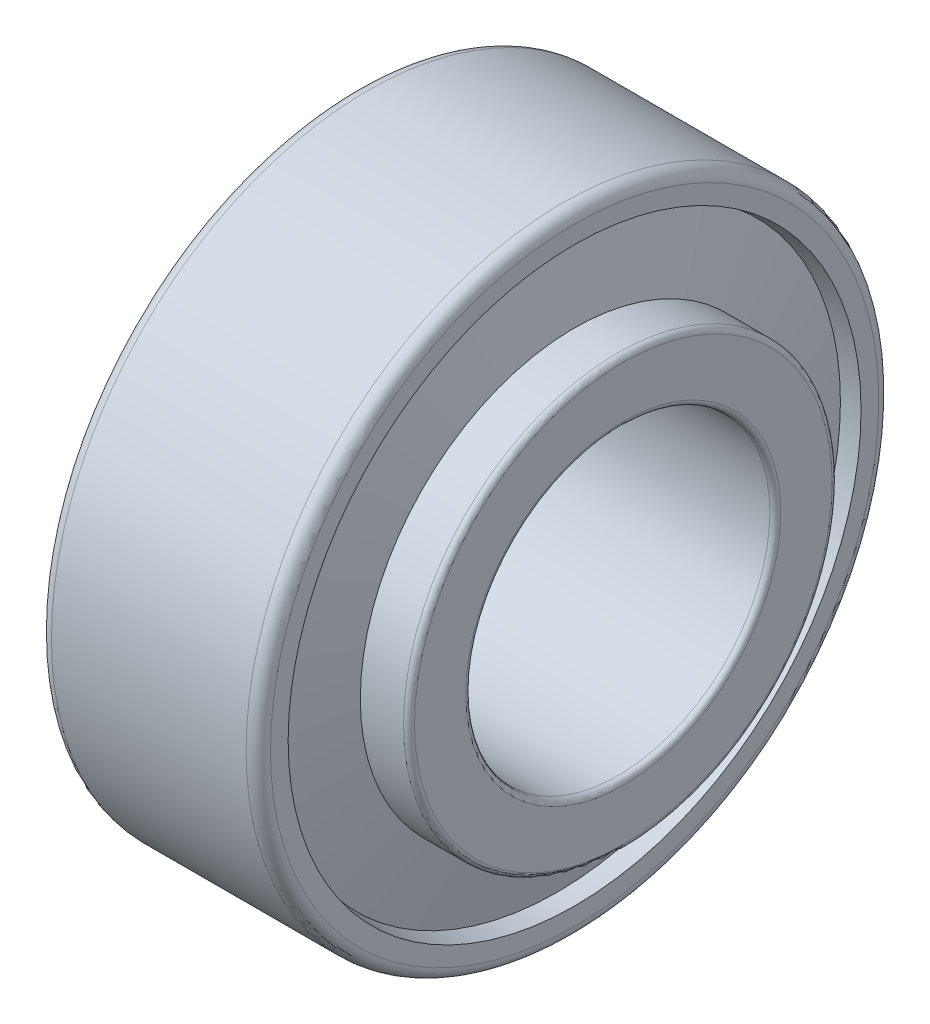
SolidWorks part; units mm, degrees
material "AISI Тип A2 Инструментальная сталь"
ref_plane "Спереди" through (0, 0, 0) normal (0, 0, 1) x (1, 0, 0)
ref_plane "Сверху" through (0, 0, 0) normal (0, 1, 0) x (1, 0, 0)
ref_plane "Справа" through (0, 0, 0) normal (1, 0, 0) x (0, 0, -1)
sketch "Эскиз1" plane through (0, 0, 0) normal (0, 0, 1) x (1, 0, 0)
  line L20 (-882.5277, 0) -> (43243.8573, 0) construction
  line L33 (1.7552, 20.5446) -> (0, 20.2205)
  line L34 (0, 20.2205) -> (0, 25)
  line L35 (1, 26) -> (17, 26)
  line L36 (18, 25) -> (18, 23.5443)
  line L37 (18, 23.5443) -> (16.5685, 23.28)
  line L38 (1.7552, 20.5446) -> (16.5685, 23.28) construction
  line L39 (3.5105, 13.0415) -> (0, 13.0415)
  line L40 (0, 13.0415) -> (0, 12.95)
  line L41 (0.45, 12.5) -> (21.55, 12.5)
  line L42 (22, 12.95) -> (22, 17.161)
  line L43 (21.55, 17.611) -> (18, 17.611)
  line L44 (18, 17.611) -> (18, 17.161)
  line L45 (3.5105, 13.0415) -> (18, 17.161) construction
  line L46 (18, 17.161) -> (16.5685, 23.28)
  line L47 (3.5105, 13.0415) -> (1.7552, 20.5446)
  line L48 (2.6329, 16.793) -> (17.2843, 20.2205) construction
  line L49 (0, 20.2205) -> (17.2843, 20.2205) construction
  line L50 (1.7552, 20.5446) -> (1.7552, 13.0415) construction
  arc A0 (0, 25) -> (1, 26) centre (1, 25) cw
  arc A1 (17, 26) -> (18, 25) centre (17, 25) cw
  arc A2 (0, 12.95) -> (0.45, 12.5) centre (0.45, 12.95) ccw
  arc A3 (22, 12.95) -> (21.55, 12.5) centre (21.55, 12.95) cw
  arc A4 (21.55, 17.611) -> (22, 17.161) centre (21.55, 17.161) cw
  point P12 (17.2843, 20.2205)
  dimension "гост r1" = 0.45
  dimension "гост r2" = 1
  dimension "гост DD" = 52
  dimension "гост B" = 22
  dimension "гост C" = 18
  dimension "гост T" = 22
  dimension "гост E" = 40.441
  dimension "гост d" = 25
  dimension "гост alfa" = 13.167
revolve "Повернуть1" add sketch "Эскиз1" angle 360 about L20
